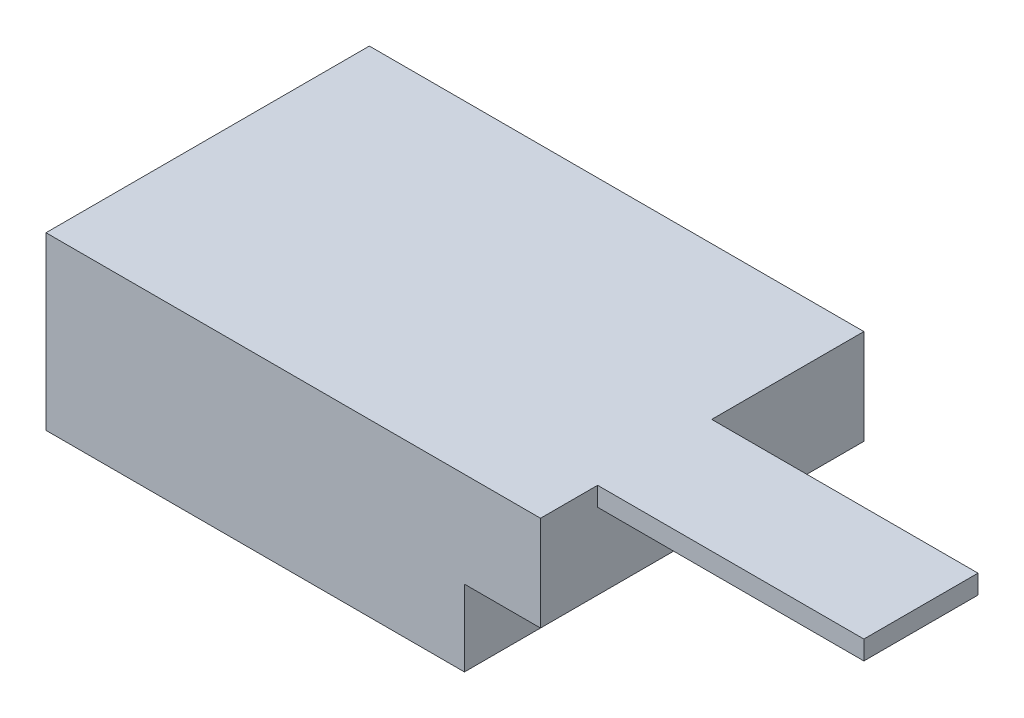
SolidWorks part; units mm, degrees
ref_plane "Front Plane" through (0, 0, 0) normal (0, 0, 1) x (1, 0, 0)
ref_plane "Top Plane" through (0, 0, 0) normal (0, 1, 0) x (1, 0, 0)
ref_plane "Right Plane" through (0, 0, 0) normal (1, 0, 0) x (0, 0, -1)
sketch "Sketch1" plane through (0, 0, 0) normal (0, 1, 0) x (1, 0, 0)
  line L1 (-41.275, -26.9875) -> (41.275, -26.9875)
  line L2 (-41.275, -26.9875) -> (-41.275, 26.9875)
  line L3 (-41.275, 26.9875) -> (41.275, 26.9875)
  line L4 (41.275, -26.9875) -> (41.275, 26.9875)
  line L5 (-41.275, -26.9875) -> (41.275, 26.9875) construction
  line L6 (-41.275, 26.9875) -> (41.275, -26.9875) construction
  point P0 (0, 0)
  dimension "D1" = 82.55
  dimension "D2" = 53.975
extrude "Boss-Extrude1" add sketch "Sketch1" along normal blind 28.575
sketch "Sketch2" plane through (0, 0, 26.9875) normal (0, 0, 1) x (1, 0, 0)
  line L0 (-41.275, 0) -> (28.575, 0) construction
  line L1 (-41.275, 0) -> (41.275, 0) construction
  line L2 (41.275, 28.575) -> (41.275, 0) construction
  line L3 (28.575, 0) -> (41.275, 0)
  line L4 (28.575, 0) -> (28.575, 12.7)
  line L5 (28.575, 12.7) -> (41.275, 12.7)
  line L6 (41.275, 0) -> (41.275, 12.7)
  dimension "D1" = 69.85
  dimension "D2" = 12.7
extrude "Cut-Extrude1" cut sketch "Sketch2" against normal through all
sketch "Sketch3" plane through (0, 28.575, 0) normal (0, 1, 0) x (1, 0, 0)
  line L0 (41.275, -26.9875) -> (41.275, -17.4625) construction
  line L1 (41.275, -26.9875) -> (41.275, 26.9875) construction
  line L3 (41.275, -17.4625) -> (85.725, -17.4625)
  line L4 (41.275, -17.4625) -> (41.275, 1.5875)
  line L5 (41.275, 1.5875) -> (85.725, 1.5875)
  line L6 (85.725, -17.4625) -> (85.725, 1.5875)
  dimension "D1" = 9.525
  dimension "D2" = 19.05
  dimension "D3" = 44.45
extrude "Boss-Extrude2" add sketch "Sketch3" against normal blind 3.175
